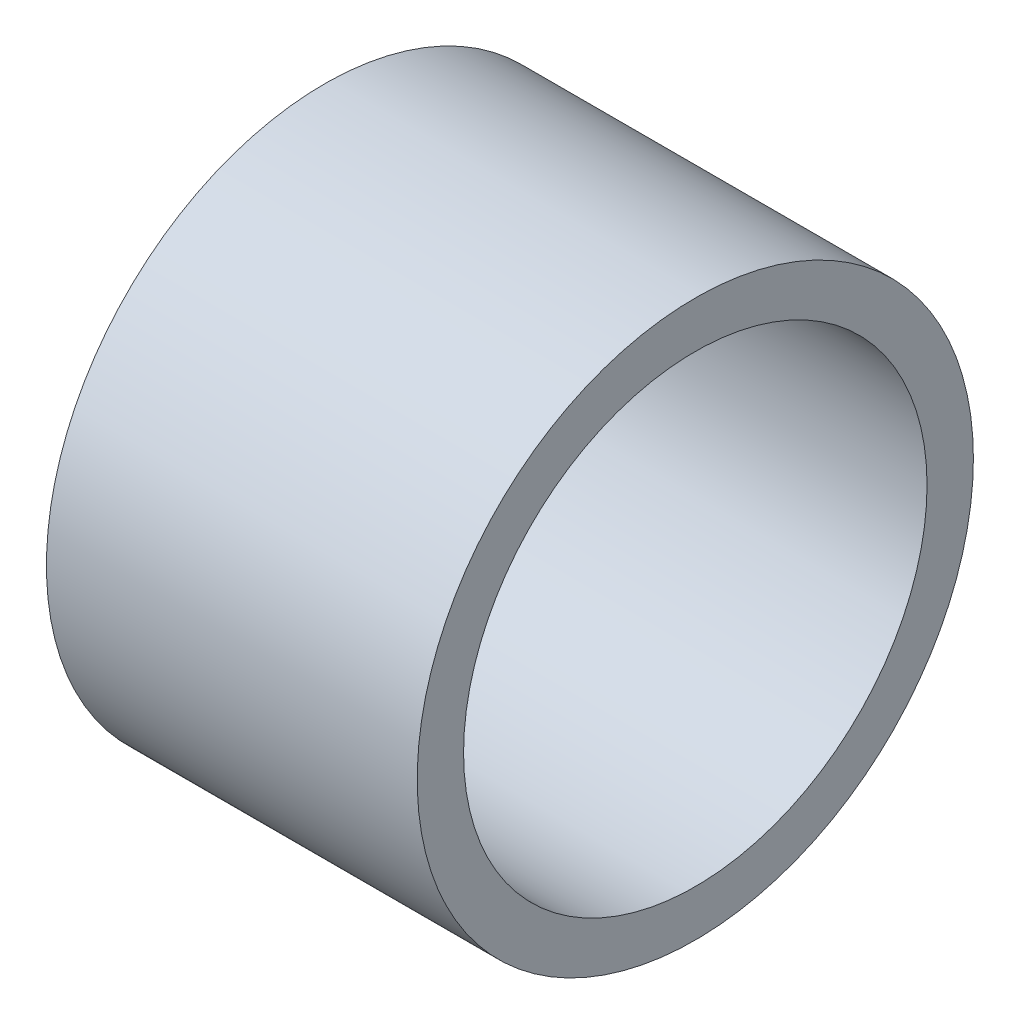
SolidWorks part; units mm, degrees
ref_plane "Спереди" through (0, 0, 0) normal (0, 0, 1) x (1, 0, 0)
ref_plane "Сверху" through (0, 0, 0) normal (0, 1, 0) x (1, 0, 0)
ref_plane "Справа" through (0, 0, 0) normal (1, 0, 0) x (0, 0, -1)
sketch "Эскиз4" plane through (0, 0, 0) normal (1, 0, 0) x (0, 0, -1)
  circle A0 centre (0, 0) radius 30
  dimension "D1" = 60
extrude "Бобышка-Вытянуть2" add sketch "Эскиз4" along normal mid plane 40
sketch "Эскиз5" plane through (20, 0, 0) normal (1, 0, 0) x (0, 0, -1)
  circle A0 centre (0, 0) radius 25
  dimension "D1" = 50
extrude "Вырез-Вытянуть2" cut sketch "Эскиз5" against normal through all
